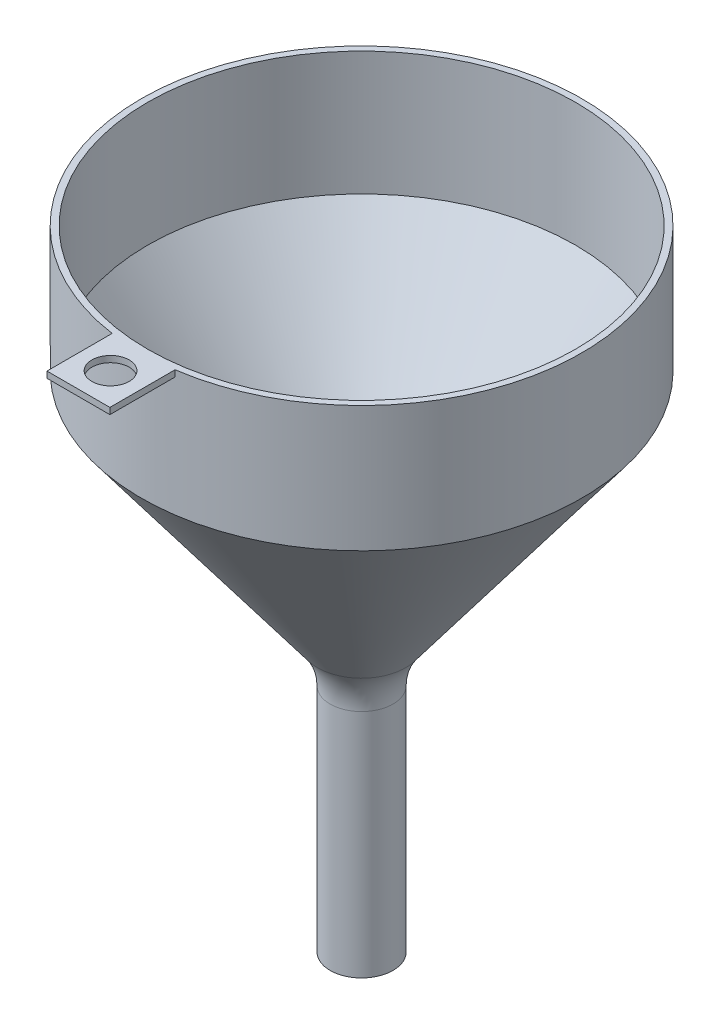
SolidWorks part; units mm, degrees
ref_plane "Alzado" through (0, 0, 0) normal (0, 0, 1) x (1, 0, 0)
ref_plane "Planta" through (0, 0, 0) normal (0, 1, 0) x (1, 0, 0)
ref_plane "Vista lateral" through (0, 0, 0) normal (1, 0, 0) x (0, 0, -1)
sketch "Croquis1" plane through (0, 0, 0) normal (0, 0, 1) x (1, 0, 0)
  line L0 (0, 100) -> (0, -100)
  line L1 (0, -100) -> (10, -100)
  line L2 (10, -100) -> (10, -20)
  line L3 (10, -20) -> (70, 60)
  line L4 (70, 100) -> (0, 100)
  line L5 (70, 60) -> (70, 100)
  line L6 (70, 100) -> (67.7486, 100.7198)
  point P3 (5, -100)
  dimension "D1" = 80
  dimension "D2" = 5
  dimension "D3" = 200
  dimension "D4" = 70
  dimension "D5" = 40
revolve "Revolución1" add sketch "Croquis1" angle 360 about L0
shell "Vaciado1" thickness 2
ref_plane "Plano1" through (0, 100, 0) normal (0, 1, 0) x (1, 0, 0)
sketch "Croquis2" plane through (0, 100, 0) normal (0, 1, 0) x (1, 0, 0)
  line L0 (0, -70) -> (0, -90)
  line L3 (10, -69.282) -> (10, -90)
  line L4 (10, -90) -> (-10, -90)
  line L5 (-10, -69.282) -> (-10, -90)
  line L6 (10, -74.5827) -> (-10, -90) construction
  line L7 (10, -90) -> (-10, -74.5827) construction
  circle A0 centre (0, 0) radius 70 construction
  arc A1 (-10, -69.282) -> (10, -69.282) centre (0, 0) ccw
  point P6 (0, -82.2913)
  point P11 (0, 0)
  point P12 (0, -90)
  dimension "D1" = 20
  dimension "D2" = 20
extrude "Saliente-Extruir1" add sketch "Croquis2" against normal blind 2 contours A1 L0 L4 L3 | A1 L5 L4 L0
sketch "Croquis3" plane through (0, 100, 0) normal (0, 1, 0) x (1, 0, 0)
  circle A0 centre (0, -79.7958) radius 5.9317
extrude "Cortar-Extruir1" cut sketch "Croquis3" against normal blind 22
ref_plane "Plano2" through (0, -100, 0) normal (0, -1, 0) x (-1, 0, 0)
sketch "Croquis4" plane through (0, -100, 0) normal (0, -1, 0) x (-1, 0, 0)
  circle A0 centre (0, 0) radius 9.2062
extrude "Cortar-Extruir2" cut sketch "Croquis4" against normal blind 82
fillet "Redondeo1" radius 20 1 edges at (-10, -20, 0)
